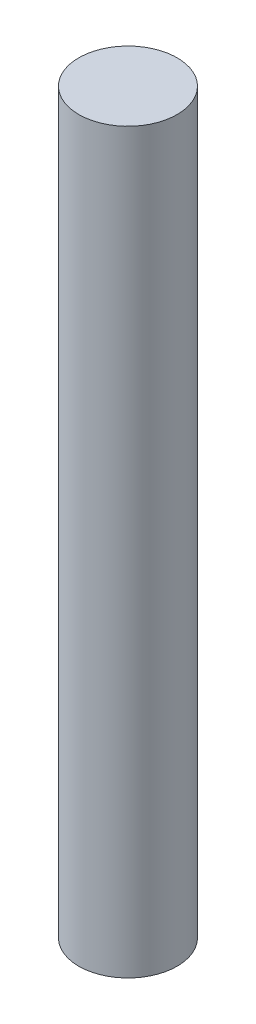
SolidWorks part; units mm, degrees
material "AISI 1020"
ref_plane "Front Plane" through (0, 0, 0) normal (0, 0, 1) x (1, 0, 0)
ref_plane "Top Plane" through (0, 0, 0) normal (0, 1, 0) x (1, 0, 0)
ref_plane "Right Plane" through (0, 0, 0) normal (1, 0, 0) x (0, 0, -1)
sketch "Sketch2" plane through (0, 0, 0) normal (0, 1, 0) x (1, 0, 0)
  circle A0 centre (0, 0) radius 3
  dimension "D1" = 6
extrude "Boss-Extrude1" add sketch "Sketch2" along normal blind 45
